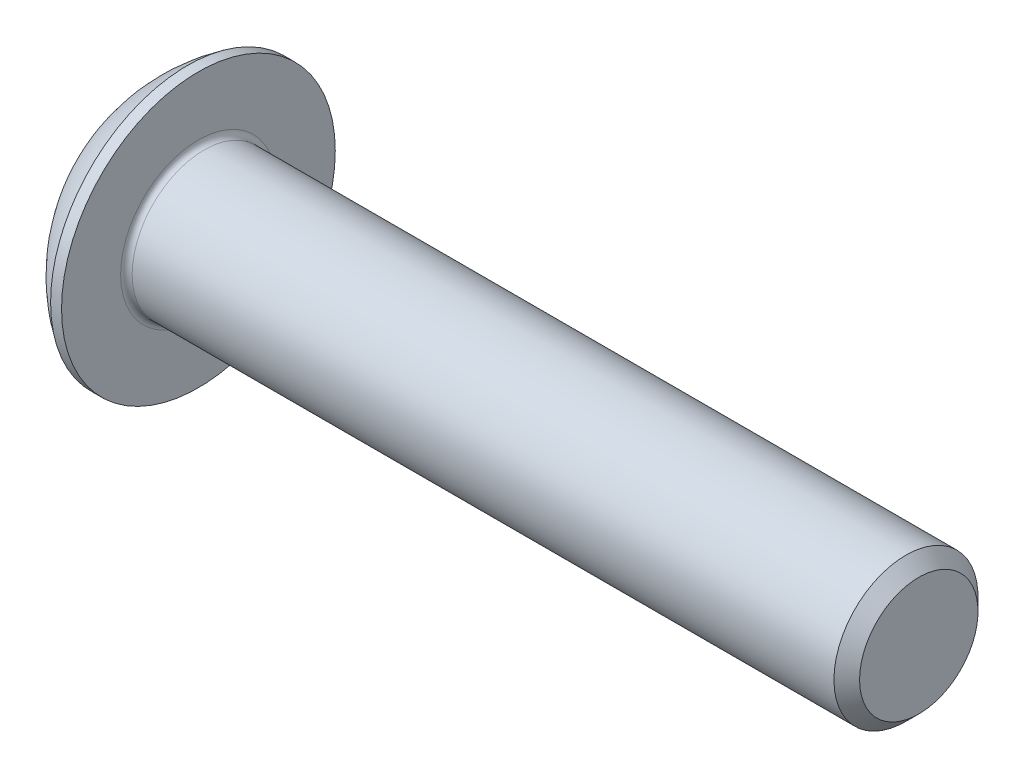
SolidWorks part; units mm, degrees
ref_plane "Plane1" through (0, 0, 0) normal (0, 0, 1) x (1, 0, 0)
ref_plane "Plane2" through (0, 0, 0) normal (0, 1, 0) x (1, 0, 0)
ref_plane "Plane3" through (0, 0, 0) normal (1, 0, 0) x (0, 0, -1)
sketch "BodySke" plane through (0, 0, 0) normal (0, 0, 1) x (1, 0, 0)
  line L0 (27.75, 0) -> (27.75, 2.055)
  line L1 (27.305, 2.5) -> (2.75, 2.5)
  line L2 (2.75, 2.5) -> (2.75, 4.75)
  line L3 (2.75, 4.75) -> (2.37, 4.75)
  line L4 (0, 0) -> (101.6, 0) construction
  line L5 (2.75, -4.75) -> (2.37, -4.75) construction
  line L6 (55.6768, -2.5) -> (2.75, -2.5) construction
  line L7 (27.75, 0) -> (0, 0)
  line L8 (0, 1.425) -> (0, -1.425) construction
  line L9 (0, 0) -> (0, 1.425)
  line L10 (27.75, 2.055) -> (27.305, 2.5)
  line L11 (27.75, -2.055) -> (27.305, -2.5) construction
  line L12 (3.55, 9.525) -> (3.55, -2.5) construction
  line L13 (2.75, 9.525) -> (2.75, -2.5) construction
  arc A1 (0, 1.425) -> (2.37, 4.75) centre (5.5166, 0) cw
  dimension "D1" = 2.85
  dimension "Head_side_ht" = 0.38
  dimension "Body_ch_ang" = 45
revolve "BaseBody" add sketch "BodySke" angle 360 about L4
cosmetic thread "ThreadCosmetic" [suppressed] parameters "Thread_length"=9, "Thread_minor"=2.439
fillet "Fillet1" radius 0.2 1 edges at (2.75, 0, 2.5)
sketch "Sketch2" plane through (0, 0, 0) normal (0, 0, 1) x (1, 0, 0)
  line L0 (0, 1.5) -> (1.56, 1.5)
  line L1 (1.56, 1.5) -> (2.426, 0)
  line L3 (2.426, 0) -> (0, 0)
  line L4 (0, 0) -> (0, 1.5)
  line L5 (0, -1.5) -> (1.56, -1.5) construction
  line L6 (0, 0) -> (47.625, 0) construction
  dimension "D2" = 60
  dimension "PreBroach_depth" = 1.56
  dimension "PreBroach_dia" = 3
revolve "PreBroach" cut sketch "Sketch2" angle 360 about L6
sketch "Sketch3" plane through (0, 0, 0) normal (1, 0, 0) x (0, 0, -1)
  line L0 (-2, -1) -> (-2, 1)
  line L1 (-2, 1) -> (0, 1)
  line L2 (0, 1) -> (1, 1)
  line L3 (1, 1) -> (1, -1)
  line L4 (1, -1) -> (0, -1)
  line L5 (0, -1) -> (-2, -1)
  dimension "D3" = 2
  dimension "D1" = 1
  dimension "D2" = 1
extrude "Hex" cut sketch "Sketch3" along normal blind 1.56
sketch "ThdSchSke" plane through (0, 0, 0) normal (0, 0, 1) x (1, 0, 0)
  line L0 (2.65, -1.2195) -> (2.4536, -1.5)
  line L1 (2.65, -1.2195) -> (2.8464, -1.5)
  line L2 (2.8464, -1.5) -> (2.8464, -1.875)
  line L3 (-3.175, 0) -> (5.1513, 0) construction
  line L5 (2.8464, -1.875) -> (2.4536, -1.875)
  line L6 (2.4536, -1.875) -> (2.4536, -1.5)
  dimension "Thread_minor" = 2.439
  dimension "SideAngle" = 55
  dimension "VeeAngle" = 70
  dimension "Overcut" = 3.75
  dimension "Diameter" = 3
  dimension "Start" = 2.65
revolve "ThreadSchematic" [suppressed] cut sketch "ThdSchSke" angle 360 about L3
pattern_linear "ThdSchPat" [suppressed]
equation "\"D1@BodySke\" = \"Head_dia@BodySke\" * .5"
equation "\"Thread_minor@ThreadCosmetic\" = \"Minor_dia@BodySke\""
equation "\"D1@Sketch3\" = \"Hex_size@Sketch3\" / 2"
equation "\"D2@Sketch3\" = \"D1@Sketch3\""
equation "\"D3@Sketch3\" = \"Hex_size@Sketch3\""
equation "\"Thread_length@ThreadCosmetic\" = ((sgn( (\"Length@BodySke\" - \"Advance@BodySke\" * 2.0) - \"Thread_nom@BodySke\" )-1)*( (\"Length@BodySke\" - \"Advance@BodySke\" * 2.0) - \"Thread_nom@BodySke\" ))/-2+ \"Thread_nom@BodySke\""
equation "\"Thread_minor@ThdSchSke\" = \"Minor_dia@BodySke\""
equation "\"Diameter@ThdSchSke\" = \"Diameter@BodySke\""
equation "\"Overcut@ThdSchSke\" = \"Diameter@BodySke\" * 1.25"
equation "\"Start@ThdSchSke\" = \"Head_ht@BodySke\" + \"Length@BodySke\" - \"Thread_length@ThreadCosmetic\"  '---Non-countersunk---"
equation "\"Num_threads@ThdSchPat\" = int( \"Thread_length@ThreadCosmetic\" / \"Advance@BodySke\" + 0.999 )  + 1"
equation "\"Advance@ThdSchPat\" = \"Thread_length@ThreadCosmetic\" /  (\"Num_threads@ThdSchPat\" - 1) 'relax it"
equation "\"Num_threads@ThdSchPat\" = \"Num_threads@ThdSchPat\" - sgn( \"Num_threads@ThdSchPat\" - 1) '---chamfered tips only---"
